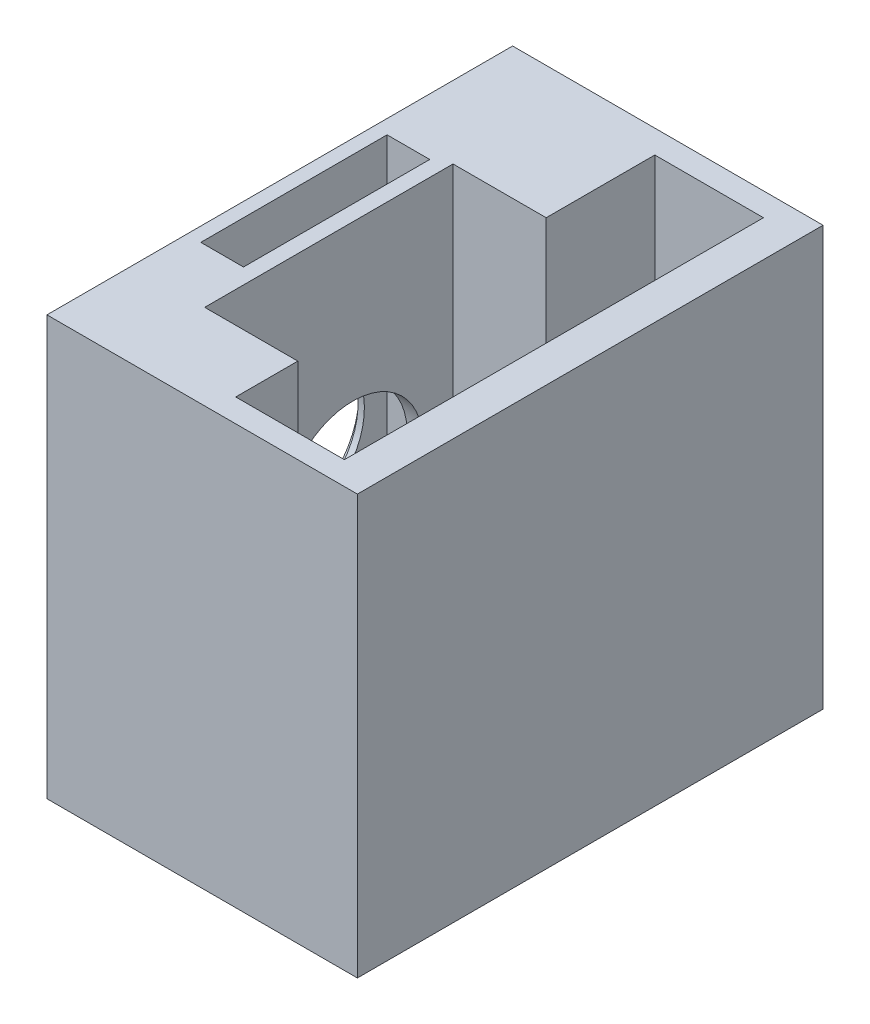
SolidWorks part; units mm, degrees
ref_plane "Front Plane" through (0, 0, 0) normal (0, 0, 1) x (1, 0, 0)
ref_plane "Top Plane" through (0, 0, 0) normal (0, 1, 0) x (1, 0, 0)
ref_plane "Right Plane" through (0, 0, 0) normal (1, 0, 0) x (0, 0, -1)
sketch "Sketch2" plane through (0, 0, 0) normal (1, 0, 0) x (0, 0, -1)
  line L1 (0, 0) -> (30, 0)
  line L2 (0, 0) -> (0, 27)
  line L3 (0, 27) -> (30, 27)
  line L4 (30, 0) -> (30, 27)
  dimension "D1" = 30
  dimension "D2" = 27
extrude "Boss-Extrude1" add sketch "Sketch2" along normal blind 20
sketch "Sketch6" plane through (2.2961, 27, -0.2935) normal (0, 1, 0) x (1, 0, 0)
  line L0 (17.7039, 29.7065) -> (-2.2961, 29.7065) construction
  line L5 (8.3658, 28.2065) -> (15.3658, 28.2065)
  line L6 (8.3658, 28.2065) -> (8.3658, 1.2065)
  line L7 (8.3658, 1.2065) -> (15.3658, 1.2065)
  line L8 (15.3658, 28.2065) -> (15.3658, 1.2065)
  dimension "D1" = 7
  dimension "D2" = 27
  dimension "D3" = 1.5
extrude "Cut-Extrude4" cut sketch "Sketch6" against normal blind 26 contours L8 L7 L6 L5
sketch "Sketch9" plane through (0, 27, 0) normal (0, 1, 0) x (1, 0, 0)
  line L0 (10.662, 28.5) -> (10.662, 1.5) construction
  line L1 (4.662, 21.5) -> (10.662, 21.5)
  line L2 (4.662, 21.5) -> (4.662, 5.5)
  line L3 (4.662, 5.5) -> (10.662, 5.5)
  line L4 (10.662, 21.5) -> (10.662, 5.5)
  line L5 (10.662, 28.5) -> (17.662, 28.5) construction
  line L6 (10.662, 1.5) -> (17.662, 1.5) construction
  dimension "D1" = 7
  dimension "D2" = 4
  dimension "D3" = 6
extrude "Cut-Extrude5" cut sketch "Sketch9" against normal blind 21
sketch "Sketch11" plane through (0, 0, 0) normal (-1, 0, 0) x (0, 0, 1)
  line L0 (-30, 27) -> (0, 27) construction
  line L1 (-30, 0) -> (-30, 27) construction
  circle A0 centre (-15.1, 12.5) radius 5
  dimension "D1" = 14.5
  dimension "D2" = 14.9
extrude "Cut-Extrude8" cut sketch "Sketch11" against normal blind 0.5
sketch "Sketch12" plane through (0, 27, 0) normal (0, 1, 0) x (1, 0, 0)
  line L0 (4.662, 21.5) -> (4.662, 5.5) construction
  line L1 (0.912, 21) -> (3.662, 21)
  line L2 (0.912, 21) -> (0.912, 9)
  line L3 (0.912, 9) -> (3.662, 9)
  line L4 (3.662, 21) -> (3.662, 9)
  line L6 (10.662, 28.5) -> (17.662, 28.5) construction
  line L7 (10.662, 1.5) -> (17.662, 1.5) construction
  point P6 (2.287, 9)
  point P9 (3.662, 15)
  dimension "D1" = 7.5
  dimension "D2" = 7.5
  dimension "D3" = 2.75
  dimension "D4" = 1
extrude "Cut-Extrude12" cut sketch "Sketch12" against normal blind 17.5
sketch "Sketch15" plane through (0.5, 0, 0) normal (-1, 0, 0) x (0, 0, 1)
  line L0 (-30, 0) -> (-30, 27) construction
  line L1 (-30, 27) -> (0, 27) construction
  circle A0 centre (-15.04, 12.5) radius 4.5
  dimension "D1" = 14.96
  dimension "D2" = 14.5
extrude "Cut-Extrude13" cut sketch "Sketch15" against normal blind 5
sketch "Sketch16" plane through (0, 0, 0) normal (0, 0, 1) x (1, 0, 0)
